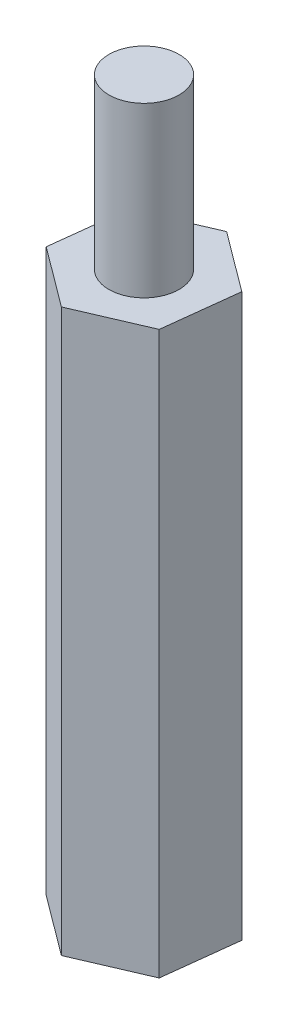
SolidWorks part; units mm, degrees
ref_plane "前视基准面" through (0, 0, 0) normal (0, 0, 1) x (1, 0, 0)
ref_plane "上视基准面" through (0, 0, 0) normal (0, 1, 0) x (1, 0, 0)
ref_plane "右视基准面" through (0, 0, 0) normal (1, 0, 0) x (0, 0, -1)
sketch "草图1" plane through (0, 0, 0) normal (0, 1, 0) x (1, 0, 0)
  line L1 (2.1251, -1.5831) -> (2.4336, 1.0488)
  line L2 (2.4336, 1.0488) -> (0.3085, 2.632)
  line L3 (0.3085, 2.632) -> (-2.1251, 1.5831)
  line L4 (-2.1251, 1.5831) -> (-2.4336, -1.0488)
  line L5 (-2.4336, -1.0488) -> (-0.3085, -2.632)
  line L6 (-0.3085, -2.632) -> (2.1251, -1.5831)
  circle A0 centre (0, 0) radius 2.295 construction
  dimension "D1" = 5.3
extrude "凸台-拉伸1" add sketch "草图1" along normal blind 20
sketch "草图2" plane through (0, 20, 0) normal (0, 1, 0) x (1, 0, 0)
  line L6 (-0.3085, -2.632) -> (2.1251, -1.5831)
  line L7 (2.1251, -1.5831) -> (2.4336, 1.0488)
  line L8 (2.4336, 1.0488) -> (0.3085, 2.632)
  line L9 (0.3085, 2.632) -> (-2.1251, 1.5831)
  line L10 (-2.1251, 1.5831) -> (-2.4336, -1.0488)
  line L11 (-2.4336, -1.0488) -> (-0.3085, -2.632)
  line L12 (-0.3085, -2.632) -> (2.1251, -1.5831)
  line L13 (2.1251, -1.5831) -> (2.4336, 1.0488)
  line L14 (2.4336, 1.0488) -> (0.3085, 2.632)
  line L15 (0.3085, 2.632) -> (-2.1251, 1.5831)
  line L16 (-2.1251, 1.5831) -> (-2.4336, -1.0488)
  line L17 (-2.4336, -1.0488) -> (-0.3085, -2.632)
  circle A0 centre (0, 0) radius 1.25
  dimension "D2" = 2.5
  dimension "D1" = 0
extrude "凸台-拉伸2" add sketch "草图2" along normal blind 6 contours A0
sketch "草图3" plane through (0, 0, 0) normal (0, -1, 0) x (1, 0, 0)
  line L6 (2.1251, 1.5831) -> (-0.3085, 2.632)
  line L7 (-0.3085, 2.632) -> (-2.4336, 1.0488)
  line L8 (-2.4336, 1.0488) -> (-2.1251, -1.5831)
  line L9 (-2.1251, -1.5831) -> (0.3085, -2.632)
  line L10 (0.3085, -2.632) -> (2.4336, -1.0488)
  line L11 (2.4336, -1.0488) -> (2.1251, 1.5831)
  line L12 (2.1251, 1.5831) -> (-0.3085, 2.632)
  line L13 (-0.3085, 2.632) -> (-2.4336, 1.0488)
  line L14 (-2.4336, 1.0488) -> (-2.1251, -1.5831)
  line L15 (-2.1251, -1.5831) -> (0.3085, -2.632)
  line L16 (0.3085, -2.632) -> (2.4336, -1.0488)
  line L17 (2.4336, -1.0488) -> (2.1251, 1.5831)
  circle A0 centre (0, 0) radius 1.25
  dimension "D2" = 2.5
  dimension "D1" = 0
extrude "切除-拉伸1" cut sketch "草图3" against normal blind 6 contours A0
